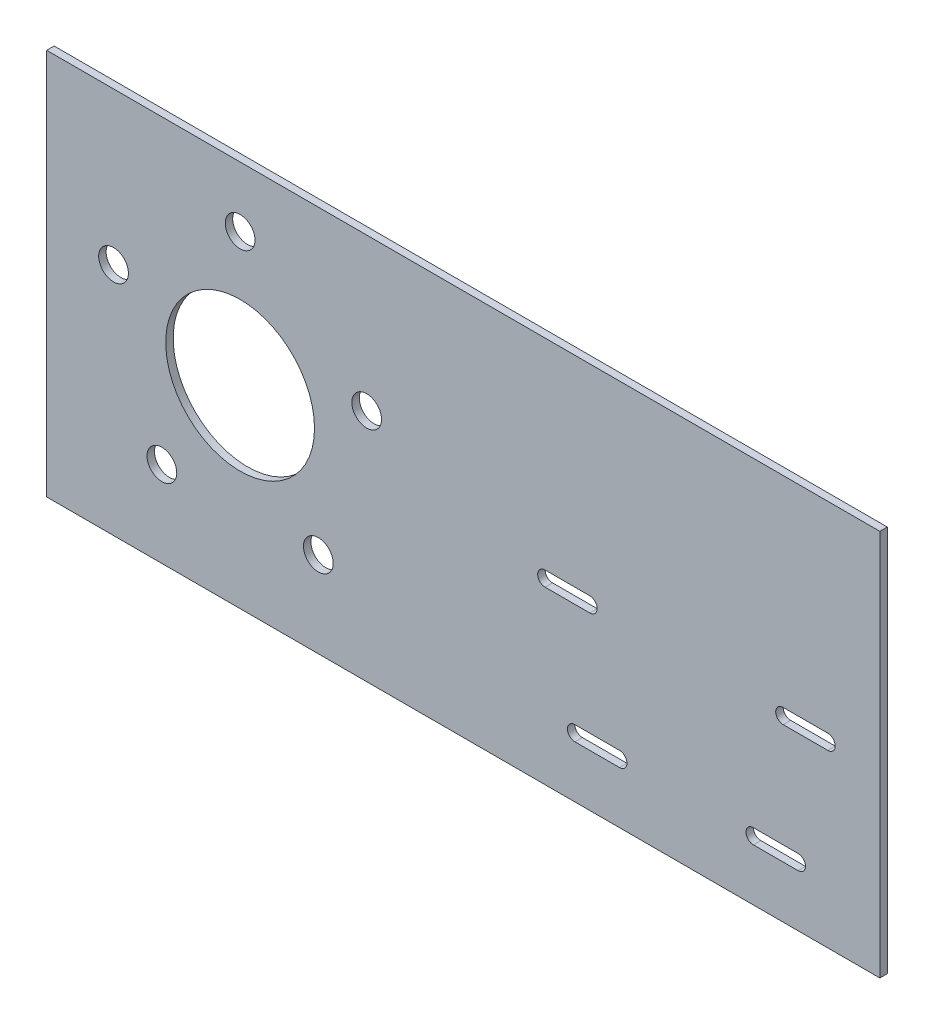
SolidWorks part; units mm, degrees
material "ASTM A36 Steel"
ref_plane "Front Plane" through (0, 0, 0) normal (0, 0, 1) x (1, 0, 0)
ref_plane "Top Plane" through (0, 0, 0) normal (0, 1, 0) x (1, 0, 0)
ref_plane "Right Plane" through (0, 0, 0) normal (1, 0, 0) x (0, 0, -1)
ref_plane "Plane1" through (190.5, 0, 0) normal (1, 0, 0) x (0, 0, -1)
sketch "Sketch1" plane through (0, 0, 0) normal (0, 0, 1) x (1, 0, 0)
  circle A2 centre (0, 0) radius 80.645
  circle A9 centre (-33.3856, -45.9513) radius 6.35
  circle A10 centre (33.3856, -45.9513) radius 6.35
  circle A11 centre (54.019, 17.5518) radius 6.35
  circle A12 centre (0, 56.7989) radius 6.35
  circle A13 centre (-54.019, 17.5518) radius 6.35
sketch "Sketch2" plane through (0, 0, 0) normal (0, 0, 1) x (1, 0, 0)
  line L0 (2.6194, 0) -> (-2.6194, 0) construction
  line L1 (273.05, -82.55) -> (-82.55, -82.55)
  line L2 (273.05, -82.55) -> (273.05, 82.55)
  line L3 (273.05, 82.55) -> (-82.55, 82.55)
  line L4 (-82.55, -82.55) -> (-82.55, 82.55)
  line L5 (273.05, -82.55) -> (-82.55, 82.55) construction
  line L6 (273.05, 82.55) -> (-82.55, -82.55) construction
  line L7 (0, -2.6194) -> (0, 2.6194) construction
  circle A0 centre (0, 0) radius 31.75
  circle A1 centre (-54.019, 17.5518) radius 6.35 construction
  circle A2 centre (0, 56.7989) radius 6.35 construction
  circle A3 centre (54.019, 17.5518) radius 6.35 construction
  circle A4 centre (33.3856, -45.9513) radius 6.35 construction
  circle A5 centre (-33.3856, -45.9513) radius 6.35 construction
  circle A6 centre (-54.019, 17.5518) radius 6.35
  circle A7 centre (0, 56.7989) radius 6.35
  circle A8 centre (54.019, 17.5518) radius 6.35
  circle A9 centre (33.3856, -45.9513) radius 6.35
  circle A10 centre (-33.3856, -45.9513) radius 6.35
  point P18 (95.25, 0)
  dimension "D1" = 63.5
  dimension "D2" = 165.1
  dimension "D3" = 82.55
  dimension "D4" = 355.6
extrude "Boss-Extrude1" add sketch "Sketch2" along normal blind 3.175
sketch "Sketch3" plane through (0, 0, 3.175) normal (0, 0, 1) x (1, 0, 0)
  line L0 (190.5, -2.6194) -> (190.5, 2.6194) construction
  line L1 (139.7, -6.35) -> (241.3, -6.35) construction
  line L2 (190.5, -6.35) -> (190.5, -57.15) construction
  line L3 (152.4, -57.15) -> (228.6, -57.15) construction
  line L4 (149.225, -6.35) -> (130.175, -6.35) construction
  line L5 (139.7, -6.35) -> (228.6, -57.15) construction
  line L6 (152.4, -57.15) -> (241.3, -6.35) construction
  line L7 (149.225, -9.525) -> (130.175, -9.525)
  line L8 (149.225, -3.175) -> (130.175, -3.175)
  line L9 (250.825, -6.35) -> (231.775, -6.35) construction
  line L10 (250.825, -9.525) -> (231.775, -9.525)
  line L11 (250.825, -3.175) -> (231.775, -3.175)
  line L12 (238.125, -57.15) -> (219.075, -57.15) construction
  line L13 (238.125, -60.325) -> (219.075, -60.325)
  line L14 (238.125, -53.975) -> (219.075, -53.975)
  line L15 (142.875, -57.15) -> (161.925, -57.15) construction
  line L16 (142.875, -53.975) -> (161.925, -53.975)
  line L17 (142.875, -60.325) -> (161.925, -60.325)
  line L18 (273.05, 82.55) -> (-82.55, 82.55) construction
  arc A0 (149.225, -9.525) -> (149.225, -3.175) centre (149.225, -6.35) ccw
  arc A1 (130.175, -3.175) -> (130.175, -9.525) centre (130.175, -6.35) ccw
  arc A2 (250.825, -9.525) -> (250.825, -3.175) centre (250.825, -6.35) ccw
  arc A3 (231.775, -3.175) -> (231.775, -9.525) centre (231.775, -6.35) ccw
  arc A4 (238.125, -60.325) -> (238.125, -53.975) centre (238.125, -57.15) ccw
  arc A5 (219.075, -53.975) -> (219.075, -60.325) centre (219.075, -57.15) ccw
  arc A6 (142.875, -53.975) -> (142.875, -60.325) centre (142.875, -57.15) ccw
  arc A7 (161.925, -60.325) -> (161.925, -53.975) centre (161.925, -57.15) ccw
  point P0 (190.5, -35.3786)
  point P11 (139.7, -6.35)
  point P18 (241.3, -6.35)
  point P23 (228.6, -57.15)
  point P30 (152.4, -57.15)
  dimension "D1" = 50.8
  dimension "D2" = 101.6
  dimension "D3" = 76.2
  dimension "D4" = 88.9
  dimension "D5" = 19.05
  dimension "D6" = 6.35
extrude "Cut-Extrude1" cut sketch "Sketch3" against normal through all
ref_plane "Plane2" through (0, -6.35, 0) normal (0, 1, 0) x (-1, 0, 0)
sketch "Sketch4" plane through (0, 0, 3.175) normal (0, 0, 1) x (1, 0, 0)
  line L0 (241.3, 57.15) -> (112.395, 57.15)
  line L1 (106.045, 50.8) -> (106.045, 28.575)
  line L2 (112.395, 22.225) -> (241.3, 22.225)
  line L3 (247.65, 28.575) -> (247.65, 50.8)
  line L4 (273.05, 82.55) -> (-82.55, 82.55) construction
  line L5 (273.05, -82.55) -> (273.05, 82.55) construction
  line L6 (149.225, -3.175) -> (130.175, -3.175) construction
  arc A0 (112.395, 57.15) -> (106.045, 50.8) centre (112.395, 50.8) ccw
  arc A1 (106.045, 28.575) -> (112.395, 22.225) centre (112.395, 28.575) ccw
  arc A2 (241.3, 22.225) -> (247.65, 28.575) centre (241.3, 28.575) ccw
  arc A3 (247.65, 50.8) -> (241.3, 57.15) centre (241.3, 50.8) ccw
  circle A5 centre (0, 0) radius 80.645 construction
  circle A6 centre (0, 0) radius 80.645
  point P21 (80.645, 0)
  dimension "D4" = 6.35
  dimension "D1" = 25.4
  dimension "D2" = 25.4
  dimension "D3" = 25.4
  dimension "D5" = 25.4
extrude "Cut-Extrude3" [suppressed] cut sketch "Sketch4" against normal through all contours L3 A3 L0 A0 L1 A1 L2 A2
sketch3d "TAG"
  line L0 (273.05, 82.55, 0) -> (-82.55, 82.55, 0) construction
  line L1 (273.05, 82.55, 3.175) -> (273.05, 82.55, 0) construction
  line L2 (273.05, -82.55, 0) -> (273.05, 82.55, 0) construction
  line L3 (273.05, 82.55, 0) -> (-82.55, 82.55, 0)
  line L4 (273.05, 82.55, 3.175) -> (273.05, 82.55, 0)
  line L5 (273.05, -82.55, 0) -> (273.05, 82.55, 0)
  dimension "D1" = 3.175
  dimension "D2" = 165.1
  dimension "D3" = 355.6
